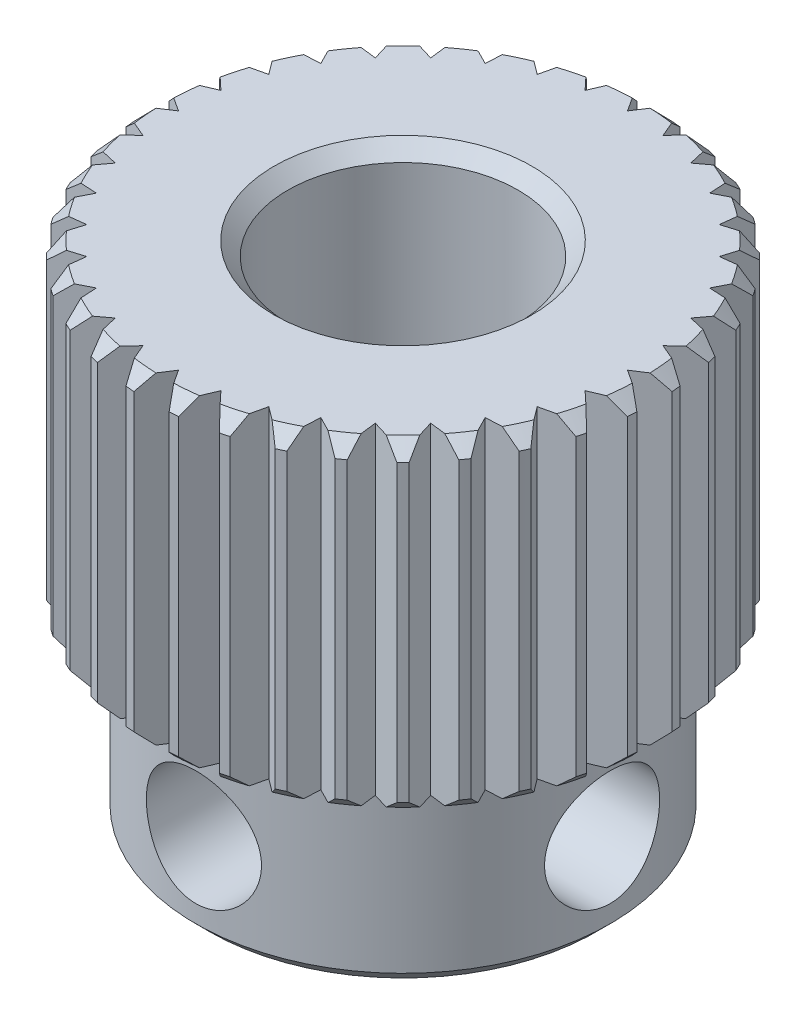
SolidWorks part; units mm, degrees
ref_plane "Front Plane" through (0, 0, 0) normal (0, 0, 1) x (1, 0, 0)
ref_plane "Top Plane" through (0, 0, 0) normal (0, 1, 0) x (1, 0, 0)
ref_plane "Right Plane" through (0, 0, 0) normal (1, 0, 0) x (0, 0, -1)
sketch "Sketch1" plane through (0, 0, 0) normal (0, 0, 1) x (1, 0, 0)
  line L0 (0, 0) -> (0, 7.8226) construction
  line L1 (2.5, -7.4) -> (2.5, 3.5)
  line L2 (2.5, 3.5) -> (5.475, 3.5)
  line L3 (5.475, 3.5) -> (5.475, -3.5)
  line L4 (5.475, -3.5) -> (4.5, -3.5)
  line L5 (4.5, -3.5) -> (4.5, -7.4)
  line L6 (4.5, -7.4) -> (2.5, -7.4)
  point P10 (5.475, 0)
  dimension "D1" = 5
  dimension "D2" = 10.95
  dimension "D3" = 10.9
  dimension "D4" = 7
  dimension "D5" = 9
revolve "Revolve1" add sketch "Sketch1" angle 360 about L0
chamfer "Chamfer1" distance 0.3 angle 45 5 edges at (0, -7.4, -2.5) (0, -7.4, -4.5) (0, 3.5, -2.5) (0, -3.5, -5.475) (0, 3.5, -5.475)
sketch "Sketch4" plane through (0, 3.5, 0) normal (0, 1, 0) x (1, 0, 0)
  line L0 (0, 0) -> (0, 6.7381) construction
  line L1 (-0.3819, 5.4617) -> (0, 4.875)
  line L2 (0, 4.875) -> (0.3819, 5.4617)
  line L3 (0, 0) -> (1.1681, 6.6244) construction
  line L4 (0, 0) -> (0.4629, 6.6199) construction
  circle A0 centre (0, 0) radius 5.475 construction
  arc A1 (0.3819, 5.4617) -> (-0.3819, 5.4617) centre (0, 0) ccw
  point P5 (0, 5.475)
  dimension "D1" = 4
  dimension "D2" = 10
  dimension "D3" = 0.6
extrude "Cut-Extrude1" cut sketch "Sketch4" against normal through all
pattern_circular "CirPattern1" count 36 over 360 about axis through (0, 0, 0) along (0, 1, 0) of "Cut-Extrude1"
sketch "Sketch5" plane through (0, 0, 0) normal (0, 0, 1) x (1, 0, 0)
  line L0 (-4.5, -7.4) -> (4.5, -7.4) construction
  circle A0 centre (0, -5.47) radius 1.25
  dimension "D1" = 1.93
  dimension "D2" = 2.5
extrude "Cut-Extrude2" cut sketch "Sketch5" along normal up to surface (4.3229 mm away)
pattern_circular "CirPattern2" count 2 every 90 about axis through (0, 0, 0) along (0, -1, 0) of "Cut-Extrude2"
